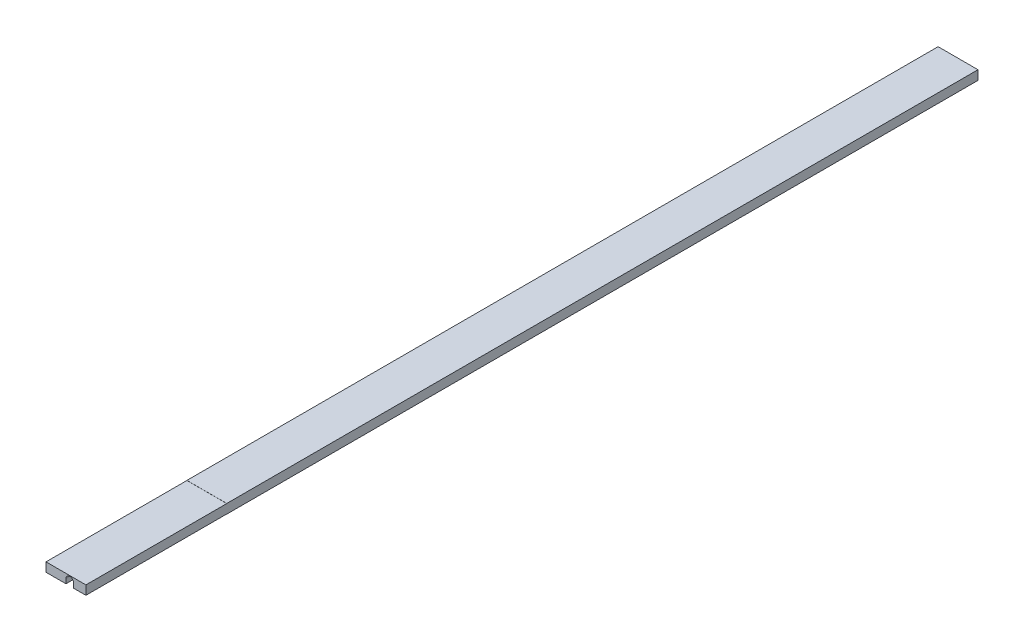
SolidWorks part; units mm, degrees
material "CFOAM 20"
ref_plane "Front Plane" through (0, 0, 0) normal (0, 0, 1) x (1, 0, 0)
ref_plane "Top Plane" through (0, 0, 0) normal (0, 1, 0) x (1, 0, 0)
ref_plane "Right Plane" through (0, 0, 0) normal (1, 0, 0) x (0, 0, -1)
sketch "Sketch1" plane through (0, 0, 0) normal (0, 0, 1) x (1, 0, 0)
  line L1 (-12.5, 2.9) -> (12.5, 2.9)
  line L2 (-12.5, 2.9) -> (-12.5, -2.9)
  line L3 (-12.5, -2.9) -> (12.5, -2.9)
  line L4 (12.5, 2.9) -> (12.5, -2.9)
  line L5 (-12.5, 2.9) -> (12.5, -2.9) construction
  line L6 (-12.5, -2.9) -> (12.5, 2.9) construction
  point P0 (0, 0)
  dimension "D1" = 25
  dimension "D2" = 5.8
extrude "Extrude1" add sketch "Sketch1" along normal mid plane 518.8
sketch "Sketch6" plane through (0, 2.9, 0) normal (0, 1, 0) x (1, 0, 0)
  line L0 (12.5, -259.4) -> (12.5, 259.4) construction
  line L1 (-12.5, 259.4) -> (12.5, 259.4)
  line L2 (-12.5, 259.4) -> (-12.5, 279.4)
  line L3 (-12.5, 279.4) -> (12.5, 279.4)
  line L4 (12.5, 259.4) -> (12.5, 279.4)
  line L5 (-12.5, -259.4) -> (12.5, -259.4)
  line L6 (-12.5, -259.4) -> (-12.5, -279.4)
  line L7 (-12.5, -279.4) -> (12.5, -279.4)
  line L8 (12.5, -259.4) -> (12.5, -279.4)
  dimension "D1" = 20
  dimension "D2" = 20
extrude "Boss-Extrude2" add sketch "Sketch6" against normal up to surface (5.8 mm away) up to face at (0, -2.9, 0)
sketch "Sketch7" plane through (0, 0, 279.4) normal (0, 0, 1) x (1, 0, 0)
  line L0 (2.381, 0.0222) -> (-12.5, 0.0222) construction
  line L1 (-12.5, -2.9) -> (-12.5, 2.9) construction
  line L2 (-12.5, 2.9) -> (12.5, 2.9) construction
  line L3 (12.5, -2.9) -> (-12.5, -2.9) construction
  line L4 (-0.0003, 0.0222) -> (-0.0003, -2.9)
  line L5 (-0.0003, -2.9) -> (4.7622, -2.9)
  line L6 (4.7622, -2.9) -> (4.7622, 0.0222)
  arc A0 (4.7622, 0.0222) -> (-0.0003, 0.0222) centre (2.381, 0.0222) ccw
  dimension "D1" = 4.7625
  dimension "D2" = 14.881
  dimension "D3" = 2.8778
extrude "Cut-Extrude2" cut sketch "Sketch7" against normal through all
sketch "Sketch8" plane through (-12.5, 0, 0) normal (-1, 0, 0) x (0, 0, 1)
  line L0 (191.15, 2.8314) -> (191.15, -2.8314) construction
  line L1 (279.4, 2.9) -> (191.15, 2.9)
  line L2 (279.4, 2.9) -> (279.4, 2.8314)
  line L3 (279.4, 2.8314) -> (191.15, 2.8314)
  line L4 (191.15, 2.9) -> (191.15, 2.8314)
  line L5 (279.4, -2.9) -> (191.15, -2.9)
  line L6 (279.4, -2.9) -> (279.4, -2.8314)
  line L7 (279.4, -2.8314) -> (191.15, -2.8314)
  line L8 (191.15, -2.9) -> (191.15, -2.8314)
  dimension "D1" = 88.25
  dimension "D2" = 0.0686
  dimension "D3" = 0.0686
extrude "Cut-Extrude3" cut sketch "Sketch8" against normal through all
